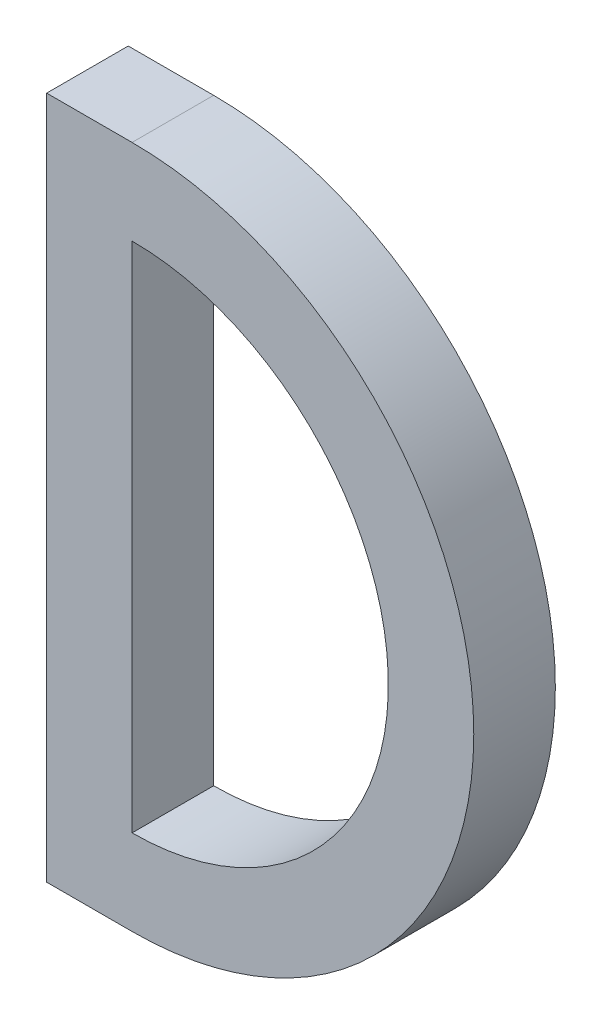
SolidWorks part; units mm, degrees
ref_plane "Front Plane" through (0, 0, 0) normal (0, 0, 1) x (1, 0, 0)
ref_plane "Top Plane" through (0, 0, 0) normal (0, 1, 0) x (1, 0, 0)
ref_plane "Right Plane" through (0, 0, 0) normal (1, 0, 0) x (0, 0, -1)
sketch "Sketch3" plane through (0, 0, 0) normal (0, 0, 1) x (1, 0, 0)
  line L0 (0, 0) -> (0, 40)
  line L1 (0, 20) -> (0, 35)
  line L2 (0, 20) -> (0, 5)
  line L3 (0, 40) -> (-5, 40)
  line L4 (-5, 40) -> (-5, 0)
  line L5 (-5, 0) -> (0, 0)
  arc A0 (0, 40) -> (0, 0) centre (0, 20) cw
  arc A1 (0, 35) -> (0, 5) centre (0, 20) cw
  point P4 (20, 20)
  point P5 (15, 20)
  dimension "D1" = 40
  dimension "D2" = 20
  dimension "D3" = 15
  dimension "D4" = 15
  dimension "D5" = 15
  dimension "D6" = 5
extrude "Boss-Extrude1" add sketch "Sketch3" along normal blind 4.7752 contours L4 L5 L0 L3 | L0 A1 A0
